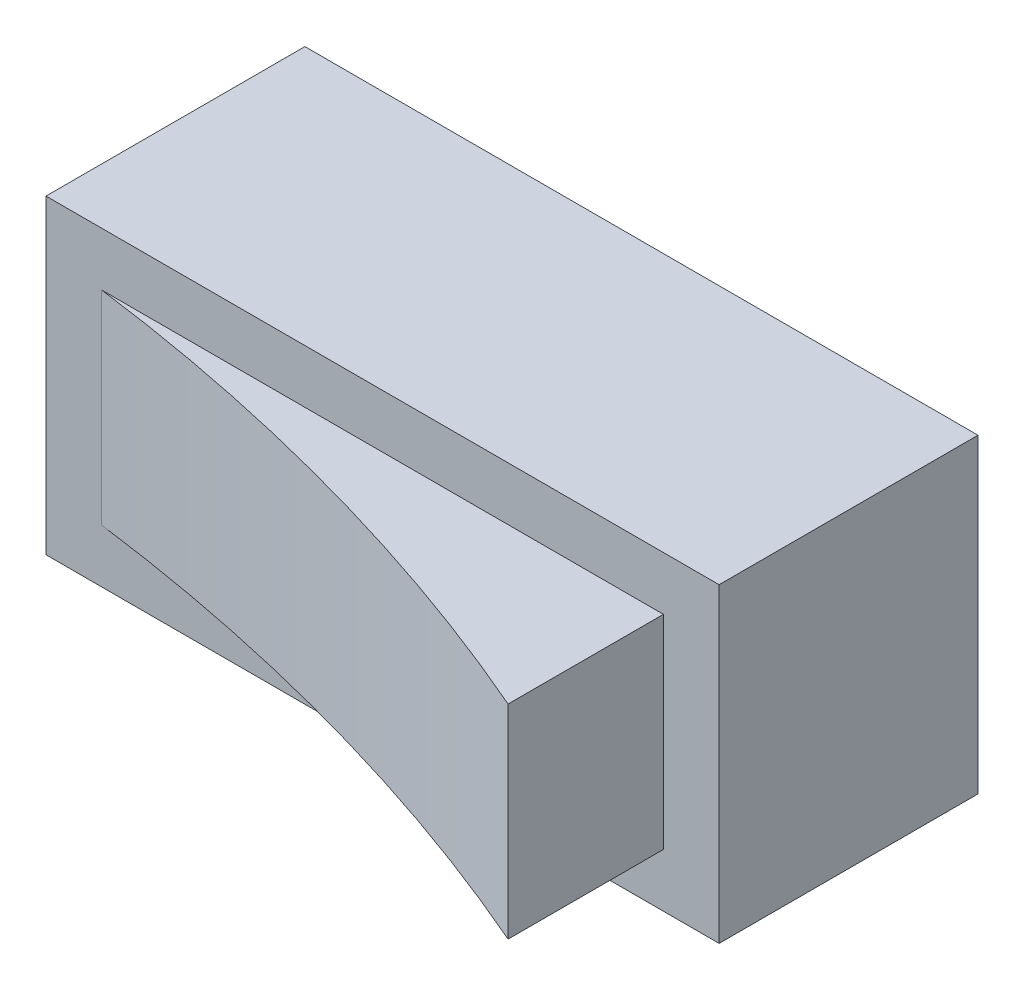
SolidWorks part; units mm, degrees
ref_plane "Front Plane" through (0, 0, 0) normal (0, 0, 1) x (1, 0, 0)
ref_plane "Top Plane" through (0, 0, 0) normal (0, 1, 0) x (1, 0, 0)
ref_plane "Right Plane" through (0, 0, 0) normal (1, 0, 0) x (0, 0, -1)
sketch "Sketch1" plane through (0, 0, 0) normal (0, 1, 0) x (1, 0, 0)
  line L1 (-3.25, 1.25) -> (3.25, 1.25)
  line L2 (-3.25, 1.25) -> (-3.25, -1.25)
  line L3 (-3.25, -1.25) -> (3.25, -1.25)
  line L4 (3.25, 1.25) -> (3.25, -1.25)
  line L5 (-3.25, 1.25) -> (3.25, -1.25) construction
  line L6 (-3.25, -1.25) -> (3.25, 1.25) construction
  point P0 (0, 0)
  dimension "D1" = 2.5
  dimension "D2" = 6.5
extrude "Boss-Extrude1" add sketch "Sketch1" along normal blind 3
sketch "Sketch2" plane through (0, 0, 1.25) normal (0, 0, 1) x (1, 0, 0)
  line L1 (-2.7122, 2.4832) -> (2.7122, 2.4832)
  line L2 (-2.7122, 2.4832) -> (-2.7122, 0.5168)
  line L3 (-2.7122, 0.5168) -> (2.7122, 0.5168)
  line L4 (2.7122, 2.4832) -> (2.7122, 0.5168)
  line L5 (-2.7122, 2.4832) -> (2.7122, 0.5168) construction
  line L6 (-2.7122, 0.5168) -> (2.7122, 2.4832) construction
  point P0 (0, 1.5)
extrude "Boss-Extrude2" add sketch "Sketch2" along normal blind 1.5
sketch "Sketch4" plane through (0, 0.5168, 0) normal (0, -1, 0) x (1, 0, 0)
  line L0 (-2.7122, 2.75) -> (2.7122, 2.75)
  line L1 (-2.7122, 2.75) -> (-2.7122, 1.25)
  arc A0 (2.7122, 2.75) -> (-2.7122, 1.25) centre (-5.3351, 21.2928) cw
extrude "Cut-Extrude1" cut sketch "Sketch4" against normal through all
